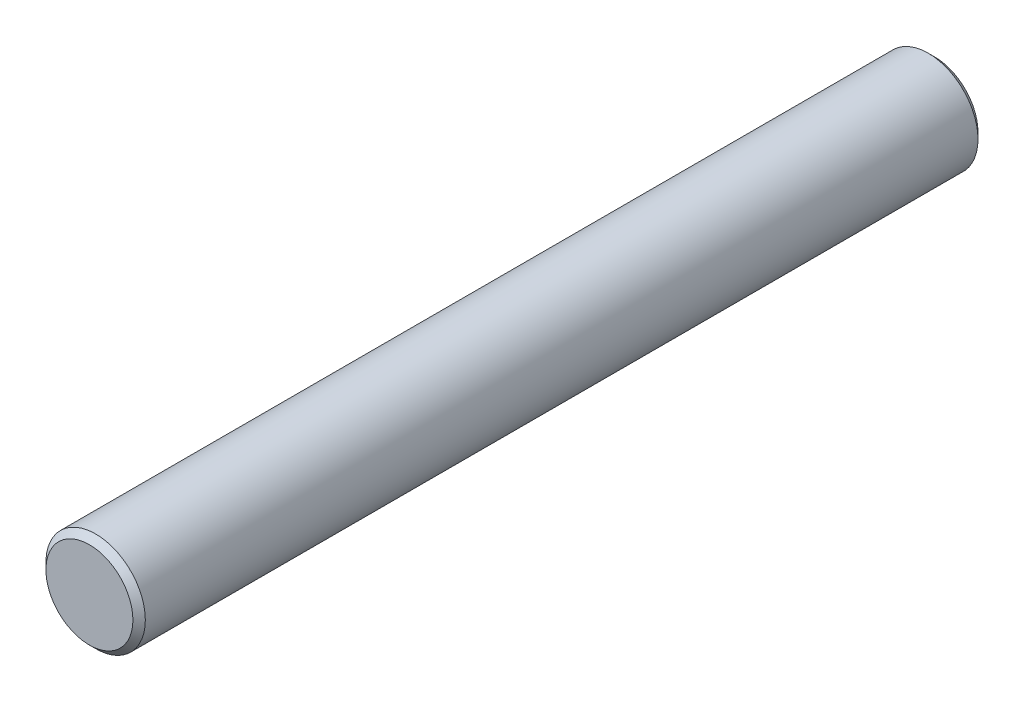
SolidWorks part; units mm, degrees
ref_plane "Front Plane" through (0, 0, 0) normal (0, 0, 1) x (1, 0, 0)
ref_plane "Top Plane" through (0, 0, 0) normal (0, 1, 0) x (1, 0, 0)
ref_plane "Right Plane" through (0, 0, 0) normal (1, 0, 0) x (0, 0, -1)
sketch "Sketch2" plane through (0, 0, 0) normal (0, 0, 1) x (1, 0, 0)
  circle A0 centre (0, 0) radius 8
  dimension "D1" = 16
extrude "Boss-Extrude1" add sketch "Sketch2" along normal mid plane 136
chamfer "Chamfer1" distance 1 angle 45 2 edges at (8, 0, -68) (8, 0, 68)
